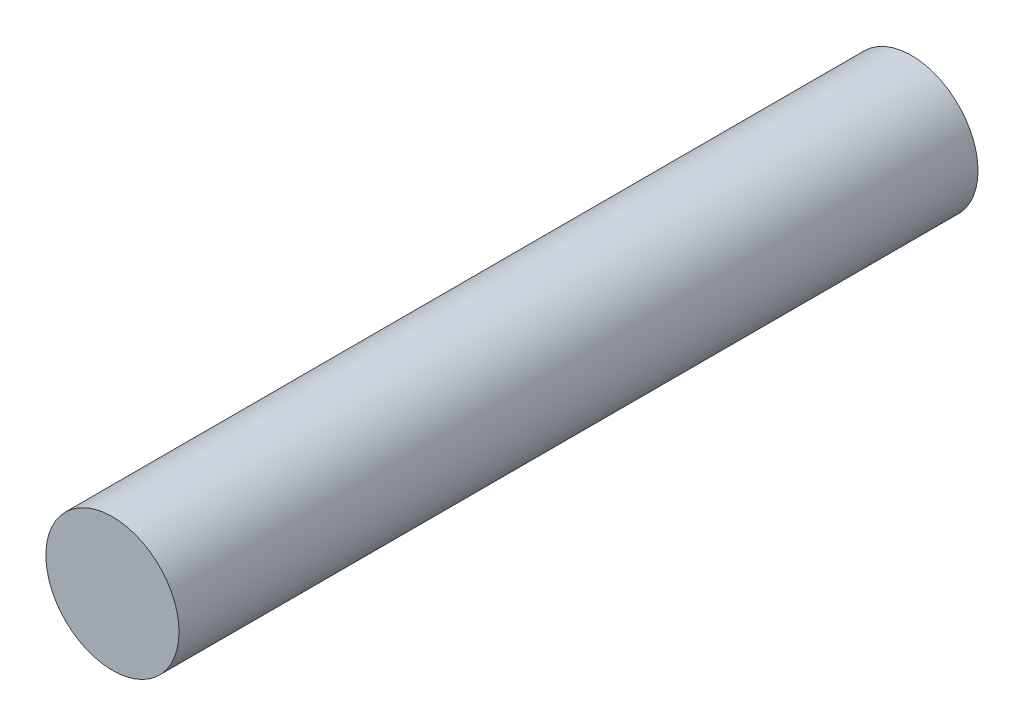
SolidWorks part; units mm, degrees
ref_plane "Front Plane" through (0, 0, 0) normal (0, 0, 1) x (1, 0, 0)
ref_plane "Top Plane" through (0, 0, 0) normal (0, 1, 0) x (1, 0, 0)
ref_plane "Right Plane" through (0, 0, 0) normal (1, 0, 0) x (0, 0, -1)
sketch "Sketch1" plane through (0, 0, 0) normal (0, 0, 1) x (1, 0, 0)
  circle A0 centre (0, 0) radius 3.175
  dimension "D1" = 6.35
extrude "Boss-Extrude1" add sketch "Sketch1" along normal blind 38.1
